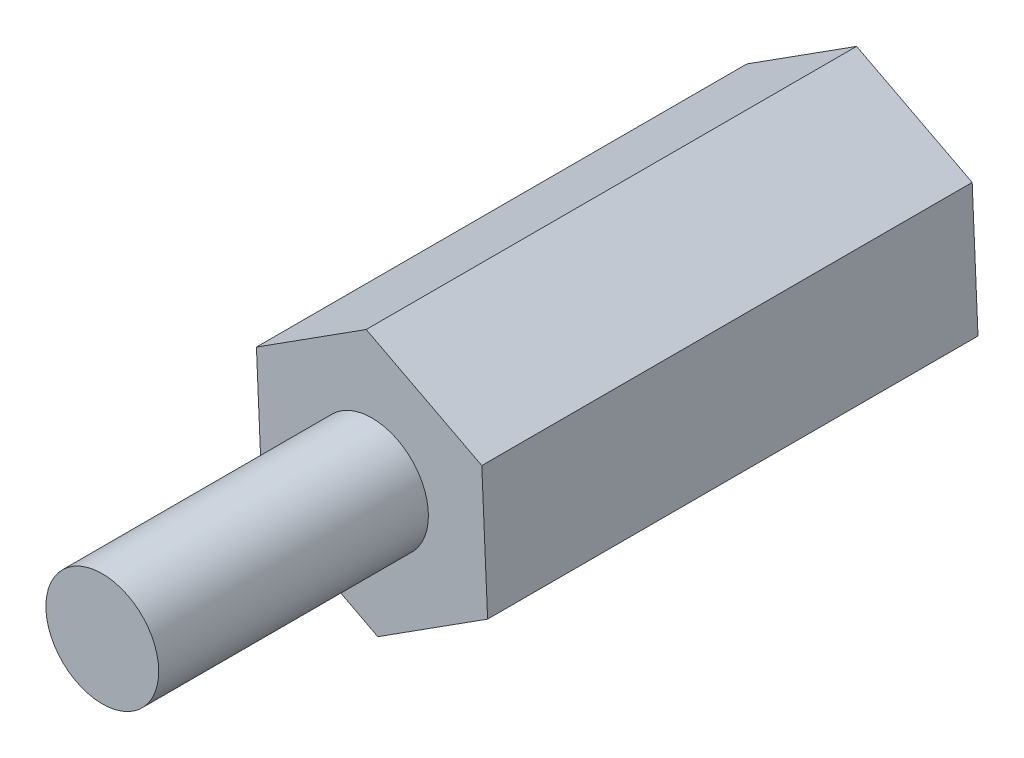
SolidWorks part; units mm, degrees
ref_plane "Front Plane" through (0, 0, 0) normal (0, 0, 1) x (1, 0, 0)
ref_plane "Top Plane" through (0, 0, 0) normal (0, 1, 0) x (1, 0, 0)
ref_plane "Right Plane" through (0, 0, 0) normal (1, 0, 0) x (0, 0, -1)
sketch "Sketch1" plane through (0, 0, 0) normal (0, 0, 1) x (1, 0, 0)
  line L1 (2.357, -1.2238) -> (2.2384, 1.4293)
  line L2 (2.2384, 1.4293) -> (-0.1186, 2.6532)
  line L3 (-0.1186, 2.6532) -> (-2.357, 1.2238)
  line L4 (-2.357, 1.2238) -> (-2.2384, -1.4293)
  line L5 (-2.2384, -1.4293) -> (0.1186, -2.6532)
  line L6 (0.1186, -2.6532) -> (2.357, -1.2238)
  circle A0 centre (0, 0) radius 2.3 construction
  circle A1 centre (0, 0) radius 1.15
extrude "Boss-Extrude1" add sketch "Sketch1" along normal blind 10
sketch "Sketch3" plane through (0, 0, 10) normal (0, 0, 1) x (1, 0, 0)
  circle A0 centre (0, 0) radius 1.15
extrude "Boss-Extrude2" add sketch "Sketch3" along normal blind 5.5 separate body
sketch "Sketch4" plane through (0, 0, 0) normal (0, 0, -1) x (-1, 0, 0)
  circle A0 centre (0, 0) radius 1.15
